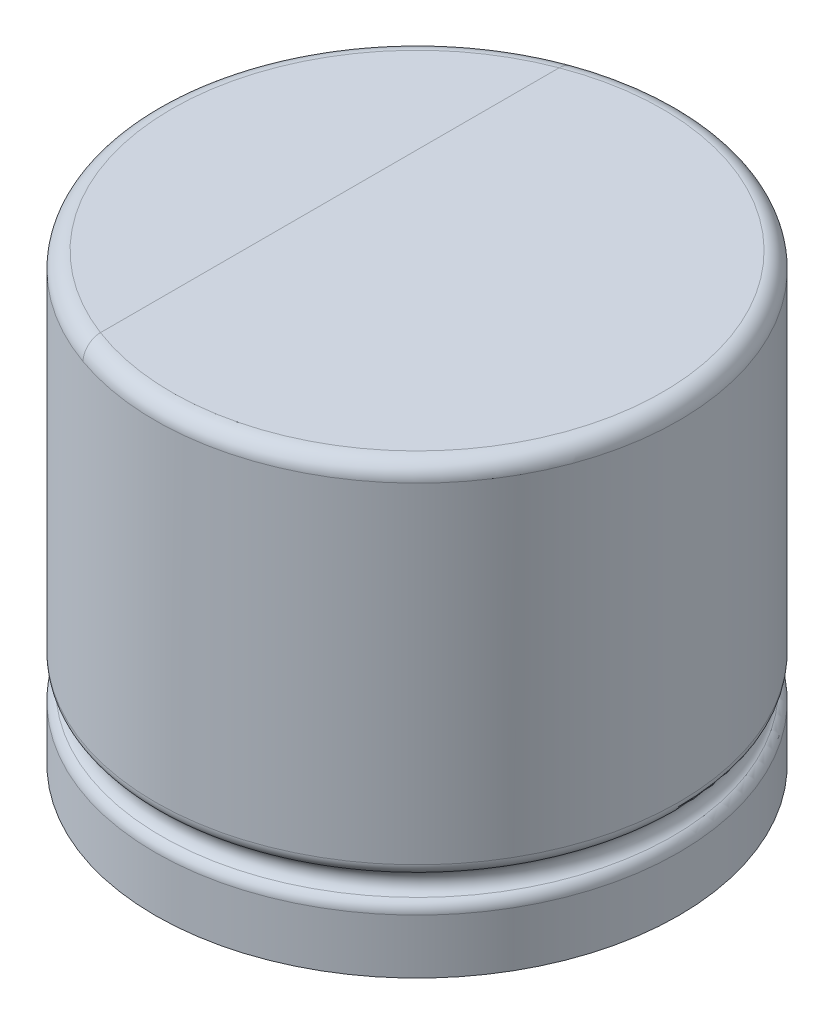
SolidWorks part; units mm, degrees
ref_plane "Alzado" through (0, 0, 0) normal (0, 0, 1) x (1, 0, 0)
ref_plane "Planta" through (0, 0, 0) normal (0, 1, 0) x (1, 0, 0)
ref_plane "Vista lateral" through (0, 0, 0) normal (1, 0, 0) x (0, 0, -1)
sketch "Croquis1" plane through (0, 0, 0) normal (0, 0, 1) x (1, 0, 0)
  line L5 (-2, 0.5) -> (-2, 0) construction
  line L7 (0, 0.5) -> (-2, 0.5)
  line L8 (0, 0.5) -> (0, 3.9)
  line L9 (0, 3.9) -> (-2, 3.9)
  line L11 (-2, 0.5) -> (-2, 3.9)
  line L15 (0, -3.9396) -> (0, 8.2908) construction
  line L16 (2, 0) -> (-2, 0) construction
  line L17 (-200002.7529, 0.5) -> (200003.228, 0.5) construction
  point P6 (0, 0)
  point P8 (0, 0)
  point P9 (0, 0)
  point P10 (0, 0)
  point P11 (0, 0)
  point P12 (0, 0)
  point P13 (0, 0)
  point P14 (-5.8856, 7.5953)
  point P15 (0, 0)
  point P20 (0, 10.2)
revolve "Revolución1" add sketch "Croquis1" angle 360 about L8
sketch "Croquis3" plane through (0, 0, 0) normal (0, 0, 1) x (1, 0, 0)
  line L0 (-1.5704, 0.6389) -> (-1.5704, 1.0833) construction
  line L5 (-1.7927, 1.0833) -> (-2, 1.0833) construction
  line L6 (-1.5704, 1.0833) -> (-1.126, 1.0833) construction
  line L9 (-2, 0.9167) -> (-2, 1.25)
  line L10 (-1.7927, 0.9722) -> (-1.9038, 0.9722) construction
  line L11 (-1.5704, 0.8611) -> (-2.0149, 0.8611) construction
  line L12 (-1.7927, 0.8611) -> (-1.7927, 1.0833) construction
  line L13 (-1.9038, 0.9722) -> (-1.9038, 0.8611) construction
  line L14 (-2, 3.9) -> (-2, 0.5) construction
  line L15 (0, -0.1687) -> (0, 0.373) construction
  line L16 (-1.9038, 0.9167) -> (-2, 0.9167) construction
  line L18 (-200002.5554, 1.25) -> (200003.4254, 1.25) construction
  line L19 (-1.9519, 0.9167) -> (-1.9519, 1.0833) construction
  line L20 (-2, 3.9) -> (-2, 0.5) construction
  line L21 (-200002.8503, 1) -> (200003.1305, 1) construction
  arc A6 (-1.9519, 1) -> (-1.9519, 1.1667) centre (-2, 1.0833) ccw
  arc A7 (-1.9519, 1) -> (-2, 0.9167) centre (-1.9038, 0.9167) ccw
  arc A8 (-1.9519, 1.1667) -> (-2, 1.25) centre (-1.9038, 1.25) cw
  point P21 (0, 0)
  point P23 (-2, 0.7385)
  point P24 (0, 0)
  point P25 (-2, 1.5786)
  point P26 (0, 0)
  point P27 (-2, 0.8077)
  point P28 (-2, 2.6157)
  point P29 (0, 0)
  point P30 (0, 0)
  point P32 (-5, 2.8114)
  point P35 (-5, 1)
  point P36 (0, 0)
  point P38 (-1.9518, 1)
  point P39 (-5, 4.8144)
  point P40 (-2, 2.451)
  point P44 (0, 0)
  point P46 (0, 0)
revolve "Cortar-Revolución1" cut sketch "Croquis3" angle 360 about L15
fillet "Redondeo1" radius 0.125 1 edges at (2, 3.9, 0)
sketch "Croquis4" plane through (0, 3.9, 0) normal (0, 1, 0) x (1, 0, 0)
  line L0 (0, 2.6904) -> (0, -3.2194) construction
  line L1 (-2, 0) -> (-0.6667, 0) construction
  line L2 (-0.6667, 0) -> (0.6667, 0) construction
  line L3 (0.6667, 0) -> (2, 0) construction
  line L4 (-2, -3.7333) -> (-2, 2.8869) construction
  line L5 (2, -3.7333) -> (2, 2.8869) construction
  line L6 (-0.6667, 1.8856) -> (-0.6667, -1.8856)
  circle A0 centre (0, 0) radius 2 construction
  point P5 (0, 0)
split line "Línea de partición1"
